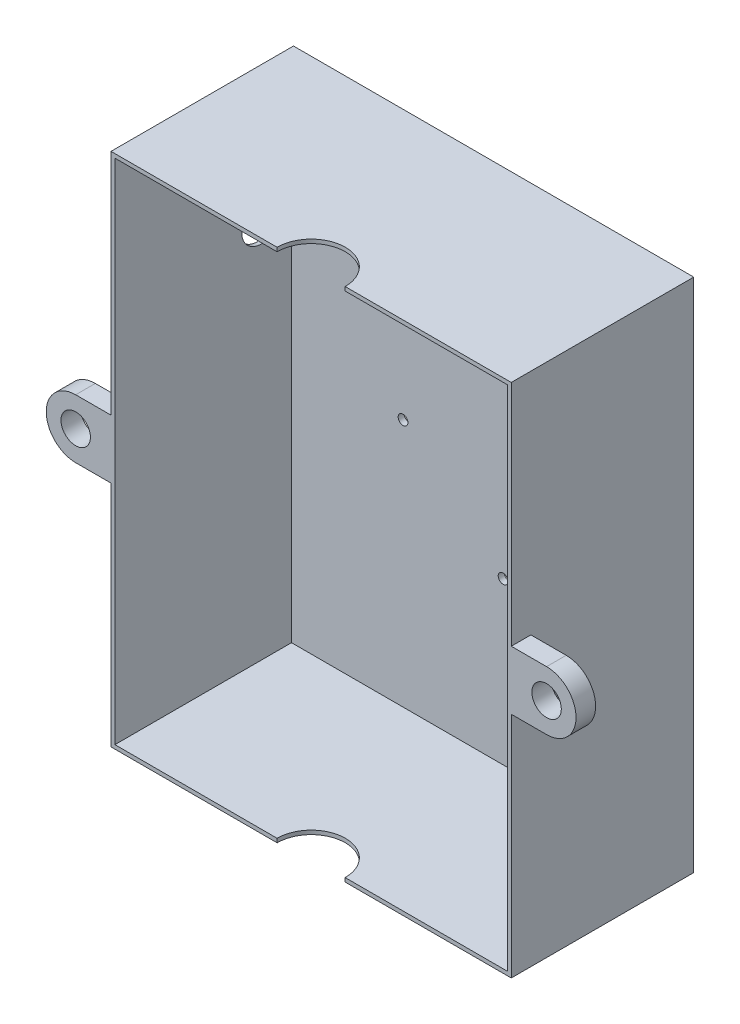
SolidWorks part; units mm, degrees
ref_plane "Front Plane" through (0, 0, 0) normal (0, 0, 1) x (1, 0, 0)
ref_plane "Top Plane" through (0, 0, 0) normal (0, 1, 0) x (1, 0, 0)
ref_plane "Right Plane" through (0, 0, 0) normal (1, 0, 0) x (0, 0, -1)
sketch "Sketch1" plane through (0, 0, 0) normal (0, 0, 1) x (-1, 0, 0)
  line L1 (98.3509, 136.1445) -> (-101.6491, 136.1445)
  line L2 (98.3509, 136.1445) -> (98.3509, -122.7351)
  line L3 (98.3509, -122.7351) -> (-101.6491, -122.7351)
  line L4 (-101.6491, 136.1445) -> (-101.6491, -122.7351)
  line L5 (98.3509, 136.1445) -> (-101.6491, -122.7351) construction
  line L6 (98.3509, -122.7351) -> (-101.6491, 136.1445) construction
extrude "Boss-Extrude1" add sketch "Sketch1" along normal blind 3
sketch "Sketch2" plane through (0, 0, 3) normal (0, 0, 1) x (1, 0, 0)
  line L0 (-98.3509, 122.7351) -> (-98.3509, -136.1445)
  line L1 (-98.3509, -136.1445) -> (101.6491, -136.1445) construction
  line L2 (-98.3509, 122.7351) -> (-98.3509, -136.1445) construction
  line L3 (-98.3509, -136.1445) -> (101.6491, -136.1445)
  line L4 (-100.3509, 122.7351) -> (-100.3509, -138.1445)
  line L5 (-100.3509, -138.1445) -> (103.6491, -138.1445)
  line L6 (103.6491, -138.1445) -> (103.6491, 124.7351)
  line L7 (103.6491, 124.7351) -> (-100.3509, 124.7351)
  line L8 (-100.3509, 124.7351) -> (-100.3509, 122.7351)
  line L9 (101.6491, -136.1445) -> (101.6491, 122.7351)
  line L10 (101.6491, 122.7351) -> (-98.3509, 122.7351)
  dimension "D1" = 2
  dimension "D2" = 2
  dimension "D3" = 2
  dimension "D4" = 2
extrude "Boss-Extrude3" add sketch "Sketch2" along normal blind 90 and the other way blind 3
sketch "Sketch3" plane through (0, 0, 0) normal (0, 0, -1) x (-1, 0, 0)
  circle A8 centre (41.5144, -9.3369) radius 2.5
  circle A9 centre (-9.4856, 35.2631) radius 2.5
  circle A10 centre (-9.4856, -53.9369) radius 2.5
  circle A11 centre (-46.9856, -20.6369) radius 2.5
extrude "Cut-Extrude2" cut sketch "Sketch3" against normal blind 3
sketch "Sketch4" plane through (0, -138.1445, 0) normal (0, -1, 0) x (1, 0, 0)
  circle A2 centre (1.6491, 92.9341) radius 17.3323
extrude "Cut-Extrude4" cut sketch "Sketch4" against normal through all
sketch "Sketch5" plane through (0, 0, 93) normal (0, 0, 1) x (1, 0, 0)
  line L1 (103.6491, -138.1445) -> (103.6491, 124.7351) construction
  line L2 (103.6491, 8.2953) -> (103.6491, -6.7047)
  line L3 (103.6491, -21.7047) -> (103.6491, -6.7047)
  line L4 (121.6491, 8.2953) -> (103.6491, 8.2953)
  line L5 (121.6491, -21.7047) -> (103.6491, -21.7047)
  line L10 (-100.3509, 124.7351) -> (-100.3509, -138.1445) construction
  line L18 (-100.3509, -21.7047) -> (-100.3509, -6.7047)
  line L19 (-100.3509, 8.2953) -> (-100.3509, -6.7047)
  line L20 (-118.3509, -21.7047) -> (-100.3509, -21.7047)
  line L21 (-118.3509, 8.2953) -> (-100.3509, 8.2953)
  arc A0 (121.6491, -21.7047) -> (121.6491, 8.2953) centre (121.6491, -6.7047) ccw
  circle A1 centre (121.6491, -6.7047) radius 7.5
  arc A8 (-118.3509, 8.2953) -> (-118.3509, -21.7047) centre (-118.3509, -6.7047) ccw
  circle A9 centre (-118.3509, -6.7047) radius 7.5
extrude "Boss-Extrude5" add sketch "Sketch5" against normal blind 10
sketch "Sketch6" plane through (-100.3509, 0, 0) normal (-1, 0, 0) x (0, 0, 1)
  circle A1 centre (18.3649, 57.5422) radius 10
extrude "Cut-Extrude5" cut sketch "Sketch6" against normal up to next
